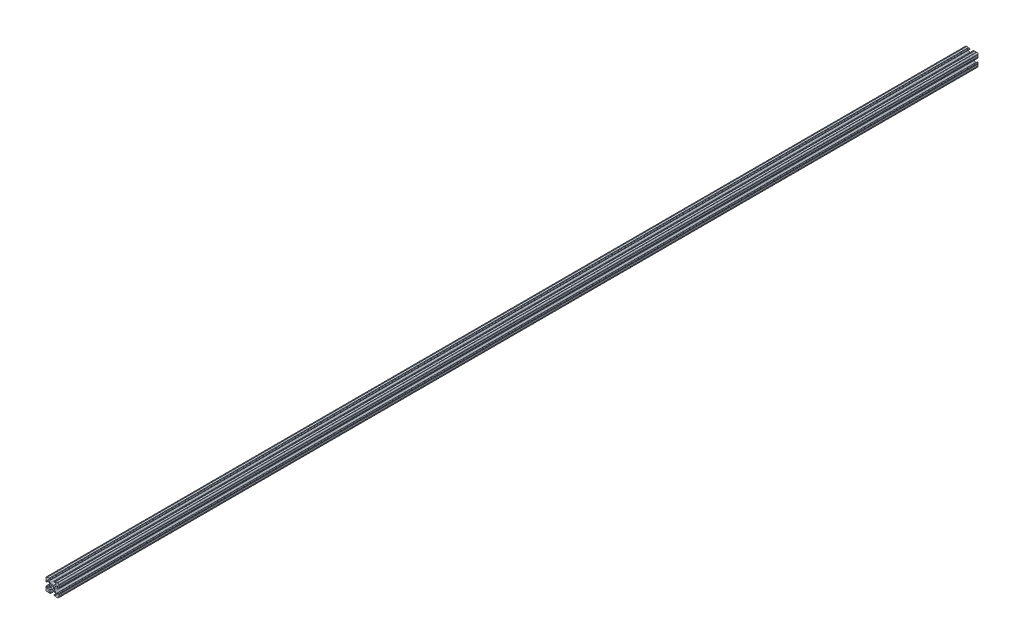
SolidWorks part; units mm, degrees
ref_plane "Front Plane" through (0, 0, 0) normal (0, 0, 1) x (1, 0, 0)
ref_plane "Top Plane" through (0, 0, 0) normal (0, 1, 0) x (1, 0, 0)
ref_plane "Right Plane" through (0, 0, 0) normal (1, 0, 0) x (0, 0, -1)
sketch "Sketch1" plane through (0, 0, 0) normal (0, 0, 1) x (1, 0, 0)
  line L88 (-7.1797, -8.6452) -> (-3.9523, -5.4237)
  line L89 (-1.7093, -4.4958) -> (1.7093, -4.4958)
  line L90 (3.9523, -5.4237) -> (7.1797, -8.6452)
  line L91 (6.4164, -10.4902) -> (4.2875, -10.4902)
  line L92 (3.2385, -11.5392) -> (3.2385, -11.651)
  line L93 (4.2875, -12.7) -> (5.3171, -12.7)
  line L94 (6.3331, -12.7) -> (9.5504, -12.7)
  line L95 (12.7, -9.5504) -> (12.7, -6.3331)
  line L96 (12.7, -5.3171) -> (12.7, -4.2875)
  line L97 (11.651, -3.2385) -> (11.5392, -3.2385)
  line L98 (10.4902, -4.2875) -> (10.4902, -6.4021)
  line L99 (8.7371, -7.1294) -> (5.441, -3.8408)
  line L100 (4.5085, -1.5932) -> (4.5085, 1.5932)
  line L101 (5.441, 3.8408) -> (8.7371, 7.1294)
  line L102 (10.4902, 6.4021) -> (10.4902, 4.2875)
  line L103 (11.5392, 3.2385) -> (11.651, 3.2385)
  line L104 (12.7, 4.2875) -> (12.7, 5.3171)
  line L105 (12.7, 6.3331) -> (12.7, 9.5504)
  line L106 (9.5504, 12.7) -> (6.3331, 12.7)
  line L107 (5.3171, 12.7) -> (4.2875, 12.7)
  line L108 (3.2385, 11.651) -> (3.2385, 11.5392)
  line L109 (4.2875, 10.4902) -> (6.4768, 10.4902)
  line L110 (7.207, 8.7244) -> (3.8983, 5.4232)
  line L111 (1.6558, 4.4958) -> (-1.6558, 4.4958)
  line L112 (-3.8983, 5.4232) -> (-7.207, 8.7244)
  line L113 (-6.4768, 10.4902) -> (-4.2875, 10.4902)
  line L114 (-3.2385, 11.5392) -> (-3.2385, 11.651)
  line L115 (-4.2875, 12.7) -> (-5.3171, 12.7)
  line L116 (-6.3331, 12.7) -> (-9.5504, 12.7)
  line L117 (-12.7, 9.5504) -> (-12.7, 6.3331)
  line L118 (-12.7, 5.3171) -> (-12.7, 4.2875)
  line L119 (-11.651, 3.2385) -> (-11.5392, 3.2385)
  line L120 (-10.4902, 4.2875) -> (-10.4902, 6.4021)
  line L121 (-8.7371, 7.1294) -> (-5.441, 3.8408)
  line L122 (-4.5085, 1.5932) -> (-4.5085, -1.5932)
  line L123 (-5.441, -3.8408) -> (-8.7371, -7.1294)
  line L124 (-10.4902, -6.4021) -> (-10.4902, -4.2875)
  line L125 (-11.5392, -3.2385) -> (-11.651, -3.2385)
  line L126 (-12.7, -4.2875) -> (-12.7, -5.3171)
  line L127 (-12.7, -6.3331) -> (-12.7, -9.5504)
  line L128 (-9.5504, -12.7) -> (-6.3331, -12.7)
  line L129 (-5.3171, -12.7) -> (-4.2875, -12.7)
  line L130 (-3.2385, -11.651) -> (-3.2385, -11.5392)
  line L131 (-4.2875, -10.4902) -> (-6.4164, -10.4902)
  circle A1 centre (0, 0) radius 2.6035
  arc A104 (-7.1797, -8.6452) -> (-6.4164, -10.4902) centre (-6.4164, -9.4098) ccw
  arc A105 (-1.7093, -4.4958) -> (-3.9523, -5.4237) centre (-1.7093, -7.6708) ccw
  arc A106 (3.9523, -5.4237) -> (1.7093, -4.4958) centre (1.7093, -7.6708) ccw
  arc A107 (6.4164, -10.4902) -> (7.1797, -8.6452) centre (6.4164, -9.4098) ccw
  arc A108 (4.2875, -10.4902) -> (3.2385, -11.5392) centre (4.2875, -11.5392) ccw
  arc A109 (3.2385, -11.651) -> (4.2875, -12.7) centre (4.2875, -11.651) ccw
  arc A110 (6.3331, -12.7) -> (5.3171, -12.7) centre (5.8251, -12.7) ccw
  arc A111 (10.5664, -12.6998) -> (9.5504, -12.7) centre (10.0584, -12.7) ccw
  arc A112 (10.5664, -12.6998) -> (12.6998, -10.5664) centre (10.5918, -10.5918) ccw
  arc A113 (12.7, -9.5504) -> (12.6998, -10.5664) centre (12.7, -10.0584) ccw
  arc A114 (12.7, -5.3171) -> (12.7, -6.3331) centre (12.7, -5.8251) ccw
  arc A115 (12.7, -4.2875) -> (11.651, -3.2385) centre (11.651, -4.2875) ccw
  arc A116 (11.5392, -3.2385) -> (10.4902, -4.2875) centre (11.5392, -4.2875) ccw
  arc A117 (8.7371, -7.1294) -> (10.4902, -6.4021) centre (9.4628, -6.4021) ccw
  arc A118 (4.5085, -1.5932) -> (5.441, -3.8408) centre (7.6835, -1.5932) ccw
  arc A119 (5.441, 3.8408) -> (4.5085, 1.5932) centre (7.6835, 1.5932) ccw
  arc A120 (10.4902, 6.4021) -> (8.7371, 7.1294) centre (9.4628, 6.4021) ccw
  arc A121 (10.4902, 4.2875) -> (11.5392, 3.2385) centre (11.5392, 4.2875) ccw
  arc A122 (11.651, 3.2385) -> (12.7, 4.2875) centre (11.651, 4.2875) ccw
  arc A123 (12.7, 6.3331) -> (12.7, 5.3171) centre (12.7, 5.8251) ccw
  arc A124 (12.6998, 10.5664) -> (12.7, 9.5504) centre (12.7, 10.0584) ccw
  arc A125 (12.6998, 10.5664) -> (10.5664, 12.6998) centre (10.5918, 10.5918) ccw
  arc A126 (9.5504, 12.7) -> (10.5664, 12.6998) centre (10.0584, 12.7) ccw
  arc A127 (5.3171, 12.7) -> (6.3331, 12.7) centre (5.8251, 12.7) ccw
  arc A128 (4.2875, 12.7) -> (3.2385, 11.651) centre (4.2875, 11.651) ccw
  arc A129 (3.2385, 11.5392) -> (4.2875, 10.4902) centre (4.2875, 11.5392) ccw
  arc A130 (7.207, 8.7244) -> (6.4768, 10.4902) centre (6.4768, 9.4563) ccw
  arc A131 (1.6558, 4.4958) -> (3.8983, 5.4232) centre (1.6558, 7.6708) ccw
  arc A132 (-3.8983, 5.4232) -> (-1.6558, 4.4958) centre (-1.6558, 7.6708) ccw
  arc A133 (-6.4768, 10.4902) -> (-7.207, 8.7244) centre (-6.4768, 9.4563) ccw
  arc A134 (-4.2875, 10.4902) -> (-3.2385, 11.5392) centre (-4.2875, 11.5392) ccw
  arc A135 (-3.2385, 11.651) -> (-4.2875, 12.7) centre (-4.2875, 11.651) ccw
  arc A136 (-6.3331, 12.7) -> (-5.3171, 12.7) centre (-5.8251, 12.7) ccw
  arc A137 (-10.5664, 12.6998) -> (-9.5504, 12.7) centre (-10.0584, 12.7) ccw
  arc A138 (-10.5664, 12.6998) -> (-12.6998, 10.5664) centre (-10.5918, 10.5918) ccw
  arc A139 (-12.7, 9.5504) -> (-12.6998, 10.5664) centre (-12.7, 10.0584) ccw
  arc A140 (-12.7, 5.3171) -> (-12.7, 6.3331) centre (-12.7, 5.8251) ccw
  arc A141 (-12.7, 4.2875) -> (-11.651, 3.2385) centre (-11.651, 4.2875) ccw
  arc A142 (-11.5392, 3.2385) -> (-10.4902, 4.2875) centre (-11.5392, 4.2875) ccw
  arc A143 (-8.7371, 7.1294) -> (-10.4902, 6.4021) centre (-9.4628, 6.4021) ccw
  arc A144 (-4.5085, 1.5932) -> (-5.441, 3.8408) centre (-7.6835, 1.5932) ccw
  arc A145 (-5.441, -3.8408) -> (-4.5085, -1.5932) centre (-7.6835, -1.5932) ccw
  arc A146 (-10.4902, -6.4021) -> (-8.7371, -7.1294) centre (-9.4628, -6.4021) ccw
  arc A147 (-10.4902, -4.2875) -> (-11.5392, -3.2385) centre (-11.5392, -4.2875) ccw
  arc A148 (-11.651, -3.2385) -> (-12.7, -4.2875) centre (-11.651, -4.2875) ccw
  arc A149 (-12.7, -6.3331) -> (-12.7, -5.3171) centre (-12.7, -5.8251) ccw
  arc A150 (-12.6998, -10.5664) -> (-12.7, -9.5504) centre (-12.7, -10.0584) ccw
  arc A151 (-12.6998, -10.5664) -> (-10.5664, -12.6998) centre (-10.5918, -10.5918) ccw
  arc A152 (-9.5504, -12.7) -> (-10.5664, -12.6998) centre (-10.0584, -12.7) ccw
  arc A153 (-5.3171, -12.7) -> (-6.3331, -12.7) centre (-5.8251, -12.7) ccw
  arc A154 (-4.2875, -12.7) -> (-3.2385, -11.651) centre (-4.2875, -11.651) ccw
  arc A155 (-3.2385, -11.5392) -> (-4.2875, -10.4902) centre (-4.2875, -11.5392) ccw
extrude "Boss-Extrude1" add sketch "Sketch1" along normal mid plane 1828.8
sketch "Sketch2" plane through (4.5085, 0, 0) normal (1, 0, 0) x (0, 0, -1)
  line L0 (-914.4, -1.5932) -> (-914.4, 1.5932) construction
  circle A0 centre (0, 0) radius 3.175
  dimension "D1" = 6.35
  dimension "D2" = 914.4
extrude "Cut-Extrude1" cut sketch "Sketch2" against normal through all and the other way through all
